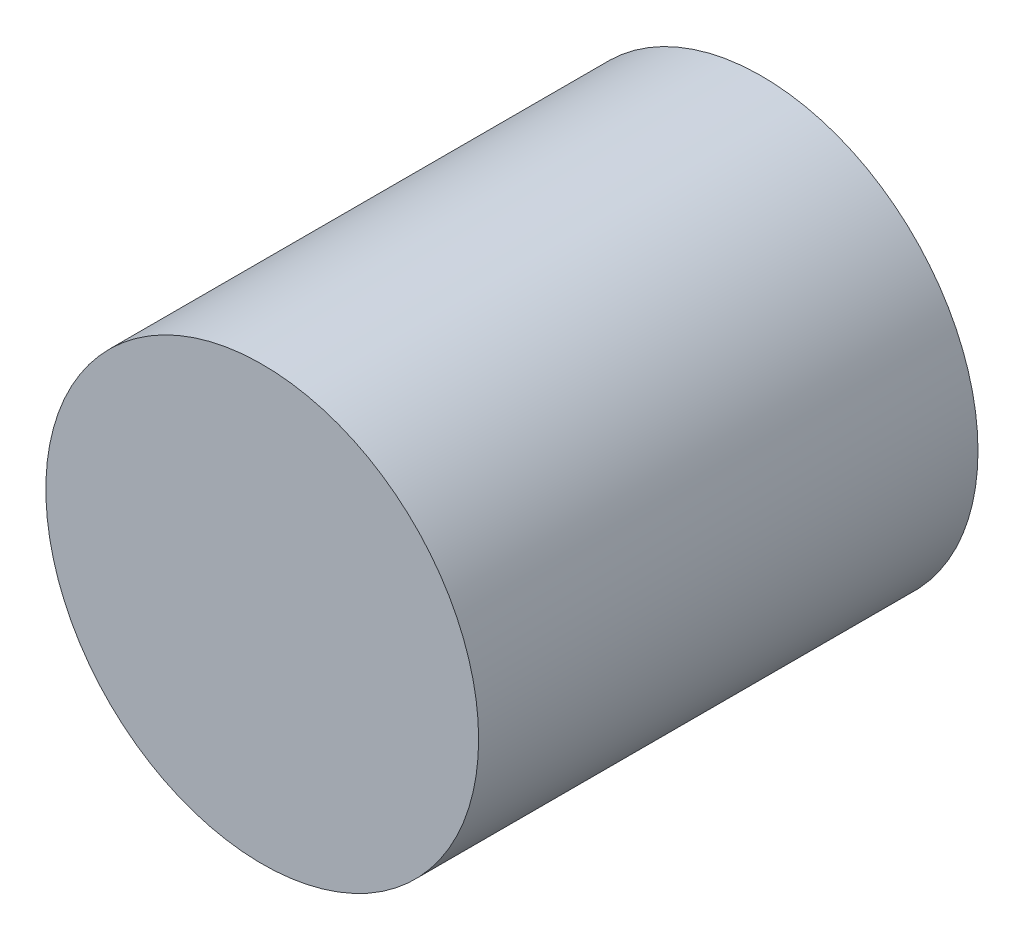
SolidWorks part; units mm, degrees
ref_plane "Front Plane" through (0, 0, 0) normal (0, 0, 1) x (1, 0, 0)
ref_plane "Top Plane" through (0, 0, 0) normal (0, 1, 0) x (1, 0, 0)
ref_plane "Right Plane" through (0, 0, 0) normal (1, 0, 0) x (0, 0, -1)
sketch "Sketch1" plane through (0, 0, 0) normal (0, 0, 1) x (1, 0, 0)
  circle A0 centre (0, 0) radius 3.9
  dimension "D1" = 7.8
extrude "Boss-Extrude1" add sketch "Sketch1" along normal blind 9
